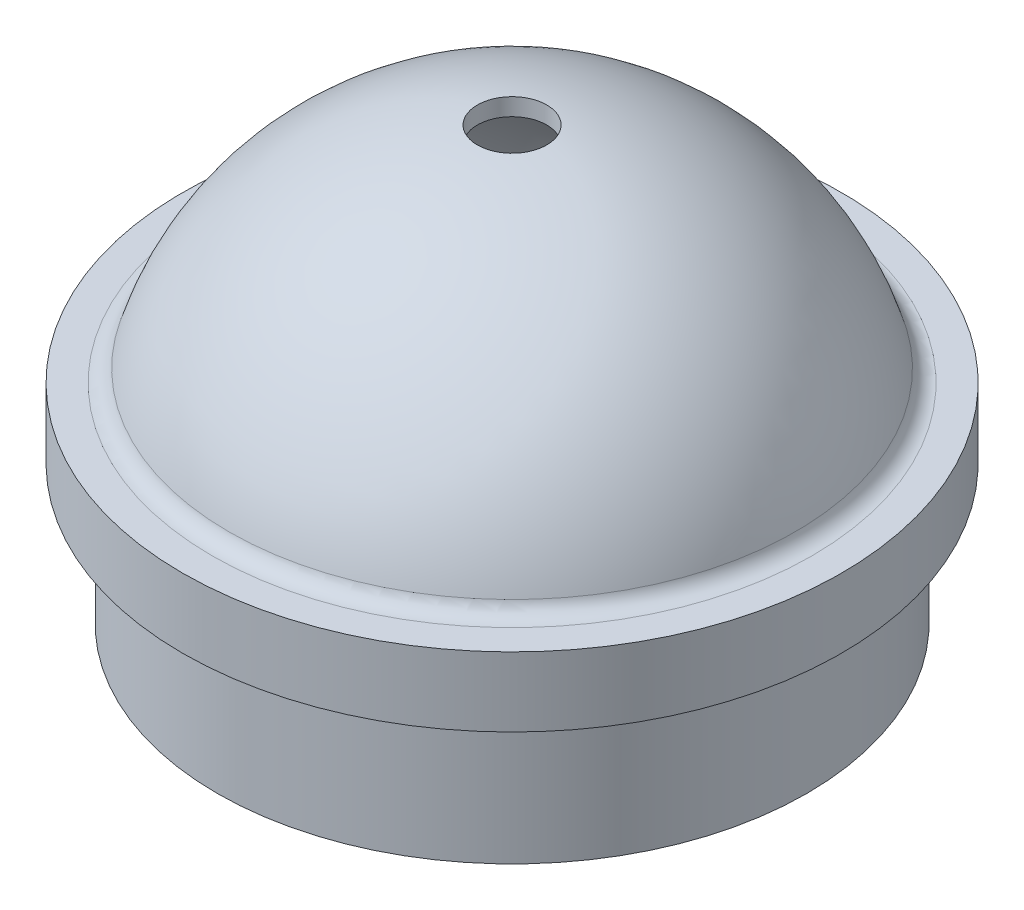
SolidWorks part; units mm, degrees
material "6061-T6 (SS)"
ref_plane "Front Plane" through (0, 0, 0) normal (0, 0, 1) x (1, 0, 0)
ref_plane "Top Plane" through (0, 0, 0) normal (0, 1, 0) x (1, 0, 0)
ref_plane "Right Plane" through (0, 0, 0) normal (1, 0, 0) x (0, 0, -1)
ref_axis "Axis1" through (0, 121.2368, 0) along (0, -1, 0)
sketch "Sketch1" plane through (0, 0, 0) normal (0, 0, 1) x (1, 0, 0)
  line L0 (-53.975, 0) -> (-53.975, 25.4)
  line L1 (91.7825, 0) -> (-91.7825, 0) construction
  line L2 (-53.975, 25.4) -> (-60.325, 25.4)
  line L3 (-6.35, 78.9766) -> (-6.35, 75.8016)
  line L4 (-50.8, 25.4) -> (-50.8, 0)
  line L5 (-53.975, 0) -> (-50.8, 0)
  line L6 (0, 121.2368) -> (0, -54.1879) construction
  line L7 (-54.8765, 38.1) -> (-60.325, 38.1)
  line L8 (-60.325, 25.4) -> (-60.325, 38.1)
  line L9 (-50.8, 25.4) -> (0, 25.4) construction
  arc A0 (-51.8265, 40.3927) -> (-6.35, 78.9766) centre (0, 25.4) cw
  arc A1 (-53.9516, 25.4) -> (-6.35, 78.9766) centre (0, 25.4) cw construction
  arc A2 (-50.8, 25.4) -> (-6.35, 75.8016) centre (0, 25.4) cw
  arc A3 (-51.8265, 40.3927) -> (-54.8765, 38.1) centre (-54.8765, 41.275) cw
  arc A5 (-50.8, 25.4) -> (-5.9791, 75.8469) centre (0, 25.4) cw construction
  point P23 (-53.975, 25.4)
  dimension "D6" = 6.35
  dimension "D8" = 25.4
  dimension "D9" = 3.175
  dimension "D10" = 6.35
  dimension "D5" = 3.175
  dimension "D2" = 50.8
  dimension "D3" = 50.8
  dimension "D7" = 12.7
  dimension "D4" = 3.175
revolve "Revolve7" add sketch "Sketch1" angle 360 about axis through (0, 121.2368, 0) along (0, -1, 0)
